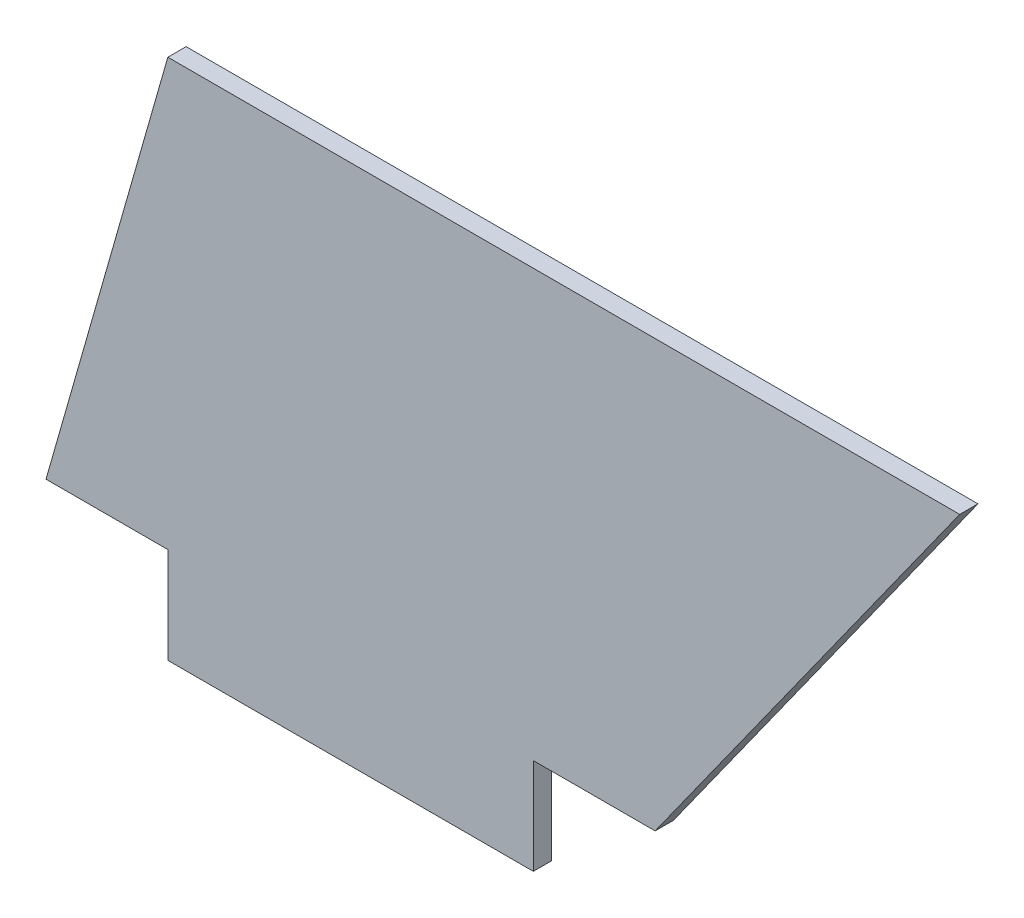
SolidWorks part; units mm, degrees
ref_plane "Front Plane" through (0, 0, 0) normal (0, 0, 1) x (1, 0, 0)
ref_plane "Top Plane" through (0, 0, 0) normal (0, 1, 0) x (1, 0, 0)
ref_plane "Right Plane" through (0, 0, 0) normal (1, 0, 0) x (0, 0, -1)
sketch "Sketch1" plane through (0, 0, 0) normal (0, 0, 1) x (1, 0, 0)
  line L0 (0, 0) -> (10, 0)
  line L1 (10, 0) -> (10, -7.875)
  line L2 (10, -7.875) -> (40, -7.875)
  line L3 (40, -7.875) -> (40, 0)
  line L4 (40, 0) -> (50, 0)
  line L5 (50, 0) -> (75, 35)
  line L6 (75, 35) -> (10, 35)
  line L7 (10, 35) -> (0, 0)
  dimension "D1" = 50
  dimension "D2" = 7.875
  dimension "D3" = 30
  dimension "D4" = 35
  dimension "D5" = 65
  dimension "D6" = 10
  dimension "D7" = 10
extrude "Boss-Extrude1" add sketch "Sketch1" along normal blind 1.5
